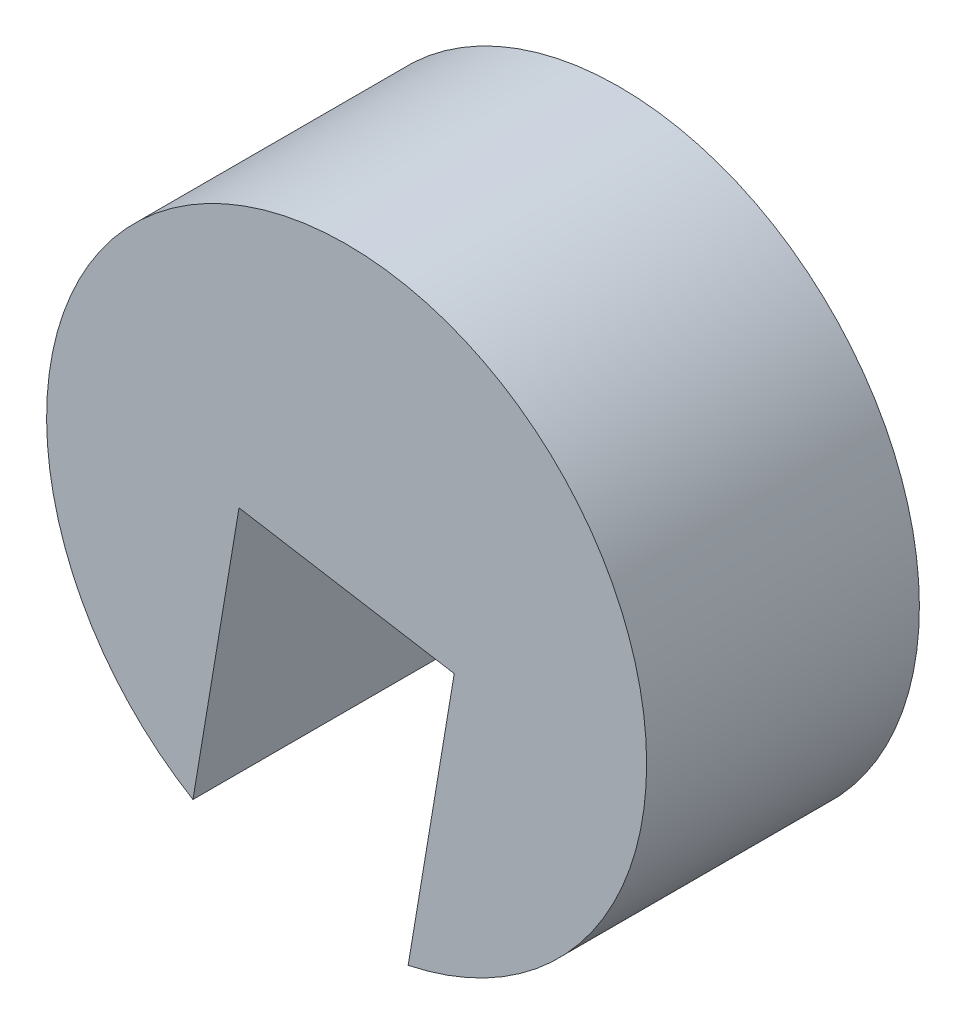
SolidWorks part; units mm, degrees
ref_plane "Front Plane" through (0, 0, 0) normal (0, 0, 1) x (1, 0, 0)
ref_plane "Top Plane" through (0, 0, 0) normal (0, 1, 0) x (1, 0, 0)
ref_plane "Right Plane" through (0, 0, 0) normal (1, 0, 0) x (0, 0, -1)
sketch "Sketch1" plane through (0, 0, 0) normal (0, 0, 1) x (1, 0, 0)
  circle A0 centre (0, 0) radius 5.5
extrude "Boss-Extrude1" add sketch "Sketch1" along normal blind 5
sketch "Sketch2" plane through (0, 0, 5) normal (0, 0, 1) x (1, 0, 0)
  line L0 (0, 0) -> (-1.9726, 0.3297)
  line L1 (0, 0) -> (1.9726, -0.3297)
  line L2 (-1.9726, 0.3297) -> (-2.8172, -4.7237)
  line L3 (1.9726, -0.3297) -> (1.1281, -5.3831)
  circle A0 centre (0, 0) radius 5.5 construction
  spline S0 degree 3 poles (-2.8172, -4.7237) (-2.3317, -5.0136) (-1.4978, -5.3497) (-0.5172, -5.4888) (0.2807, -5.5101) (0.7578, -5.4608) (1.1281, -5.3831) knots 0 0 0 0 0.414681 0.650713 0.722389 1 1 1 1
extrude "Cut-Extrude3" cut sketch "Sketch2" against normal blind 5
